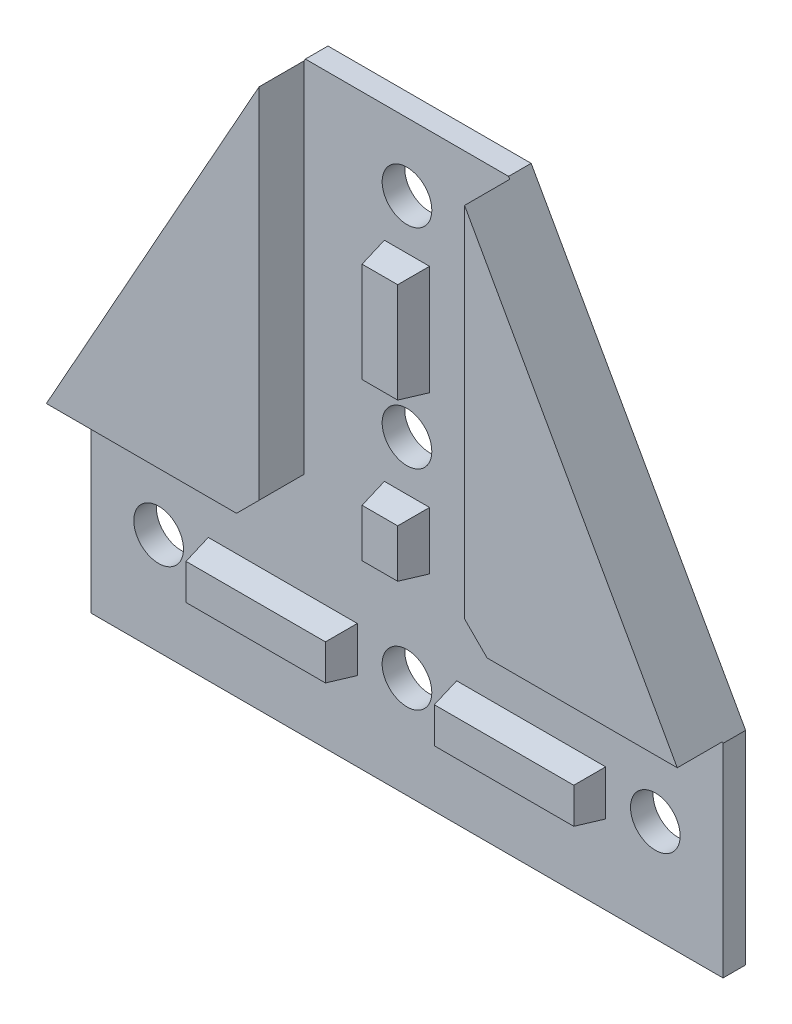
SolidWorks part; units mm, degrees
ref_plane "Plan de face" through (0, 0, 0) normal (0, 0, 1) x (1, 0, 0)
ref_plane "Plan de dessus" through (0, 0, 0) normal (0, 1, 0) x (1, 0, 0)
ref_plane "Plan de droite" through (0, 0, 0) normal (1, 0, 0) x (0, 0, -1)
sketch "Esquisse1" plane through (0, 0, 0) normal (0, 0, 1) x (1, 0, 0)
  line L0 (-22.5, 75.2324) -> (22.5, 75.2324)
  line L1 (22.5, 75.2324) -> (70, -9.7676)
  line L2 (70, -9.7676) -> (70, -54.7676)
  line L3 (70, -54.7676) -> (-70, -54.7676)
  line L4 (0, -54.7676) -> (0, 75.2324) construction
  line L5 (-70, -9.7676) -> (-70, -54.7676)
  line L6 (-22.5, 75.2324) -> (-70, -9.7676)
  line L7 (70, -32.2676) -> (-70, -32.2676) construction
  circle A0 centre (0, 60.2324) radius 5.5
  circle A1 centre (0, 13.9824) radius 5.5
  circle A2 centre (0, -32.2676) radius 5.5
  circle A3 centre (-55, -32.2676) radius 5.5
  circle A4 centre (55, -32.2676) radius 5.5
  dimension "D5" = 11
  dimension "D6" = 11
  dimension "D7" = 11
  dimension "D8" = 22.5
  dimension "D9" = 92.5
  dimension "D10" = 15
  dimension "D11" = 11
  dimension "D12" = 15
  dimension "D13" = 15
  dimension "D14" = 11
  dimension "D15" = 46.25
  dimension "D1" = 22.5
  dimension "D2" = 45
  dimension "D3" = 130
  dimension "D4" = 70
extrude "Boss.-Extru.1" add sketch "Esquisse1" along normal blind 5
sketch "Esquisse2" plane through (0, 0, 5) normal (0, 0, 1) x (1, 0, 0)
  line L0 (0, 60.2324) -> (0, -32.2676) construction
  line L1 (-55, -32.2676) -> (55, -32.2676) construction
  line L2 (-70, -54.7676) -> (70, -54.7676) construction
  line L3 (-44, -27.2676) -> (-11, -27.2676)
  line L4 (-44, -27.2676) -> (-44, -37.2676)
  line L5 (-44, -37.2676) -> (-11, -37.2676)
  line L6 (-11, -27.2676) -> (-11, -37.2676)
  line L7 (11, -27.2676) -> (44, -27.2676)
  line L8 (11, -27.2676) -> (11, -37.2676)
  line L9 (11, -37.2676) -> (44, -37.2676)
  line L10 (44, -27.2676) -> (44, -37.2676)
  line L11 (-5, 49.2324) -> (5, 49.2324)
  line L12 (-5, 49.2324) -> (-5, 24.9824)
  line L13 (-5, 24.9824) -> (5, 24.9824)
  line L14 (5, 49.2324) -> (5, 24.9824)
  line L15 (-5, 2.9824) -> (5, 2.9824)
  line L16 (-5, 2.9824) -> (-5, -9.7676)
  line L17 (-5, -9.7676) -> (5, -9.7676)
  line L18 (5, 2.9824) -> (5, -9.7676)
  circle A0 centre (0, 13.9824) radius 5.5 construction
  point P24 (0, 13.9824)
  dimension "D1" = 10
  dimension "D2" = 5
  dimension "D3" = 11
  dimension "D4" = 45
  dimension "D5" = 10
  dimension "D6" = 11
  dimension "D7" = 11
  dimension "D8" = 5
  dimension "D9" = 10
  dimension "D10" = 5
  dimension "D11" = 11
  dimension "D12" = 11
  dimension "D13" = 10
  dimension "D14" = 11
  dimension "D15" = 5
  dimension "D16" = 11
extrude "Boss.-Extru.2" add sketch "Esquisse2" along normal blind 6
draft "Dépouille1" type of draft neutral plane draft angle 10 faces to draft 16 face at (44, -32.2676, 8) face at (27.5, -27.2676, 8) face at (-11, -32.2676, 8) face at (-27.5, -27.2676, 8) face at (0, 2.9824, 8) face at (5, -3.3926, 8) face at (0, 49.2324, 8) face at (5, 37.1074, 8) face at (-5, 37.1074, 8) face at (0, 24.9824, 8) face at (11, -32.2676, 8) face at (-44, -32.2676, 8) face at (-5, -3.3926, 8) face at (-27.5, -37.2676, 8) face at (27.5, -37.2676, 8) face at (0, -9.7676, 8) neutral plane through (0, 0, 5) neutral plane normal (0, 0, 1) parameters "D1"=10
sketch "Esquisse3" plane through (0, 0, 5) normal (0, 0, 1) x (1, 0, 0)
  line L0 (-22.75, 74.7851) -> (-22.75, -9.5176)
  line L1 (-22.75, -9.5176) -> (-69.8603, -9.5176)
  line L2 (0, 75.2324) -> (0, -32.2676) construction
  line L3 (22.5, 75.2324) -> (-22.5, 75.2324) construction
  line L4 (-69.8603, -9.5176) -> (-22.75, 74.7851)
  line L5 (22.75, -9.5176) -> (69.8603, -9.5176)
  line L6 (22.75, 74.7851) -> (22.75, -9.5176)
  line L7 (69.8603, -9.5176) -> (22.75, 74.7851)
  line L8 (-22.5, 75.2324) -> (-70, -9.7676) construction
  circle A0 centre (-55, -32.2676) radius 5.5 construction
  dimension "D1" = 22.75
  dimension "D2" = 22.75
extrude "Boss.-Extru.3" add sketch "Esquisse3" along normal blind 10
chamfer "Chanfrein1" distance 5 angle 45 2 edges at (22.75, -9.5176, 10) (-22.75, -9.5176, 10)
